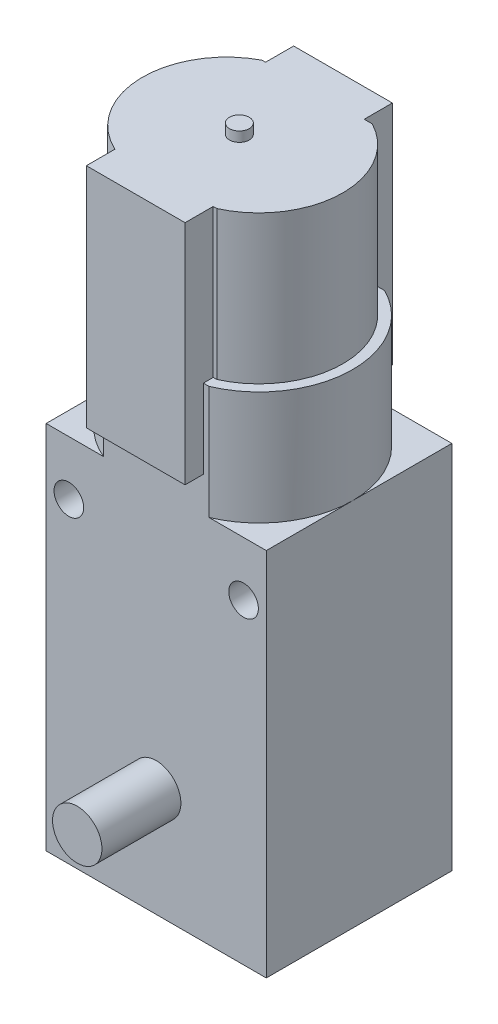
SolidWorks part; units mm, degrees
ref_plane "前视基准面" through (0, 0, 0) normal (0, 0, 1) x (1, 0, 0)
ref_plane "上视基准面" through (0, 0, 0) normal (0, 1, 0) x (1, 0, 0)
ref_plane "右视基准面" through (0, 0, 0) normal (1, 0, 0) x (0, 0, -1)
sketch "草图1" plane through (0, 0, 0) normal (0, 1, 0) x (1, 0, 0)
  line L0 (0, 0) -> (11.492, 0) construction
  line L1 (0, 0) -> (0, -13.6468) construction
  line L3 (-11.15, 9.4) -> (11.15, 9.4)
  line L4 (-11.15, 9.4) -> (-11.15, -9.4)
  line L5 (-11.15, -9.4) -> (11.15, -9.4)
  line L6 (11.15, 9.4) -> (11.15, -9.4)
  line L7 (-11.15, 9.4) -> (11.15, -9.4) construction
  line L8 (-11.15, -9.4) -> (11.15, 9.4) construction
  point P4 (0, 0)
  dimension "D1" = 22.3
  dimension "D2" = 18.8
extrude "凸台-拉伸1" add sketch "草图1" along normal blind 37.5
sketch "草图2" plane through (0, 37.5, 0) normal (0, 1, 0) x (1, 0, 0)
  line L0 (11.15, -9.4) -> (-11.15, 7.9) construction
  line L1 (11.15, -9.4) -> (-11.15, -9.4)
  line L2 (11.15, -9.4) -> (11.15, -0.6398)
  line L3 (11.15, 7.9) -> (-11.15, 7.9)
  line L4 (11.15, -9.4) -> (11.15, 9.4)
  line L5 (11.15, 9.4) -> (-11.15, 9.4)
  line L6 (-11.15, 9.4) -> (-11.15, -9.4)
  line L7 (-11.15, -9.4) -> (11.15, -9.4)
  line L8 (11.15, -9.4) -> (11.15, 9.4)
  line L9 (11.15, 9.4) -> (-11.15, 9.4)
  line L10 (-11.15, 9.4) -> (-11.15, -9.4)
  line L11 (-11.15, -9.4) -> (11.15, -9.4)
  line L12 (-11.15, -9.4) -> (-11.15, 7.9)
  line L13 (-11.15, -9.4) -> (11.15, 7.9) construction
  line L14 (-11.1286, -0.0014) -> (-11.15, 0)
  line L15 (0, -0.75) -> (0, 7.9)
  arc A1 (5.8274, 7.9) -> (5.3447, -9.4) centre (1.6378, -0.6398) cw
  arc A2 (-5.8274, 7.9) -> (-5.3447, -9.4) centre (-1.6378, -0.6398) ccw
  line M9 (11.15, -9.4) -> (11.15, 9.4)
  line M11 (-11.15, 9.4) -> (-11.15, -9.4)
  line M12 (-11.15, -9.4) -> (11.15, -9.4)
  dimension "D2" = 1.5
  dimension "D1" = 0
extrude "凸台-拉伸2" add sketch "草图2" along normal blind 11.5 contours L3 M9 M11 M12
sketch "草图3" plane through (0, 49, 0) normal (0, 1, 0) x (1, 0, 0)
  line L7 (-5.3447, -9.4) -> (5.3447, -9.4)
  line L10 (-5.1359, -8.4) -> (5.1359, -8.4)
  line L15 (5.5885, 6.9) -> (-5.5885, 6.9)
  line L17 (-5.3447, -8.4) -> (5.3447, -8.4) construction
  line L23 (-5.3447, -9.4) -> (5.3447, -9.4)
  line L28 (5.3447, -9.4) -> (-5.3447, -9.4)
  line L30 (5.3447, -9.4) -> (-5.3447, -9.4)
  line L34 (5.8274, 7.9) -> (-5.8274, 7.9)
  arc A0 (5.8274, 7.9) -> (5.3447, -9.4) centre (1.6378, -0.6398) cw
  arc A1 (-5.8274, 7.9) -> (-5.3447, -9.4) centre (-1.6378, -0.6398) ccw
  arc A2 (5.5885, 6.9) -> (5.1359, -8.4) centre (1.6378, -0.6398) cw
  arc A3 (-5.5885, 6.9) -> (-5.1359, -8.4) centre (-1.6378, -0.6398) ccw
  arc A5 (5.5885, 6.9) -> (4.955, -8.4791) centre (1.6378, -0.6398) cw construction
  arc A6 (-5.5885, 6.9) -> (-4.955, -8.4791) centre (-1.6378, -0.6398) ccw construction
  point P6 (0, -1.0733)
  dimension "D1" = 1
extrude "凸台-拉伸3" add sketch "草图3" along normal blind 15
sketch "草图6" plane through (0, 64, 0) normal (0, 1, 0) x (1, 0, 0)
  circle A1 centre (-0.2263, -0.75) radius 1
extrude "凸台-拉伸5" add sketch "草图6" along normal blind 1
sketch "草图7" plane through (0, 0, 0) normal (0, -1, 0) x (1, 0, 0)
  line L0 (-11.15, 9.4) -> (11.15, -7.9) construction
  line L1 (-11.15, 9.4) -> (11.15, 9.4)
  line L2 (-11.15, 9.4) -> (-11.15, 0.6398)
  line L3 (-11.15, -7.9) -> (11.15, -7.9)
  line L4 (-11.15, 9.4) -> (-11.15, -9.4)
  line L5 (-11.15, -9.4) -> (11.15, -9.4)
  line L6 (11.15, -9.4) -> (11.15, 9.4)
  line L7 (11.15, 9.4) -> (-11.15, 9.4)
  line L8 (11.15, 9.4) -> (11.15, -7.9)
  line L9 (11.15, 9.4) -> (-11.15, -7.9) construction
  line L10 (11.1286, 0.0014) -> (11.15, 0)
  line L11 (0, 0.75) -> (0, -7.9)
  line L13 (2.5, 2.25) -> (-2.5, 2.25)
  line L14 (2.5, 2.25) -> (2.5, -0.75)
  line L15 (2.5, -0.75) -> (-2.5, -0.75)
  line L16 (-2.5, 2.25) -> (-2.5, -0.75)
  line L17 (2.5, 2.25) -> (-2.5, -0.75) construction
  line L18 (2.5, -0.75) -> (-2.5, 2.25) construction
  arc A0 (-5.8274, -7.9) -> (-5.3447, 9.4) centre (-1.6378, 0.6398) cw
  arc A1 (5.8274, -7.9) -> (5.3447, 9.4) centre (1.6378, 0.6398) ccw
  dimension "D1" = 3
  dimension "D2" = 5
extrude "凸台-拉伸6" add sketch "草图7" along normal blind 5 contours L14 L15 L16 L13
sketch "草图8" plane through (0, 0, 2.25) normal (0, 0, 1) x (1, 0, 0)
  line L0 (-2.5, 0) -> (2.5, -5)
  circle A0 centre (0, -2.5) radius 1.5
  dimension "D1" = 3
extrude "切除-拉伸1" cut sketch "草图8" against normal through all contours L0 A0 | L0 A0
sketch "草图9" plane through (0, 0, -9.4) normal (0, 0, -1) x (-1, 0, 0)
  line L0 (-11.15, 0) -> (11.15, 0) construction
  line L1 (-2.6, 11) -> (0, 13.6)
  line L3 (2.6, 11) -> (0, 8.4)
  line L4 (-11.15, 37.5) -> (11.15, 37.5)
  line L5 (-11.15, 37.5) -> (-11.15, 0)
  line L6 (-11.15, 0) -> (11.15, 0)
  line L7 (11.15, 37.5) -> (11.15, 0)
  arc A0 (-2.6, 11) -> (0, 8.4) centre (0, 11) ccw
  circle A1 centre (0, 11) radius 1
  arc A2 (2.6, 11) -> (0, 13.6) centre (0, 11) ccw
  dimension "D1" = 11
extrude "凸台-拉伸7" add sketch "草图9" along normal blind 8 contours L3 A2 L1 A0 A1
sketch "草图10" plane through (0, 0, 9.4) normal (0, 0, 1) x (1, 0, 0)
  line L2 (-11.15, 37.5) -> (11.15, 37.5)
  line L3 (-11.15, 37.5) -> (-11.15, 0)
  line L4 (-11.15, 0) -> (11.15, 0)
  line L5 (11.15, 37.5) -> (11.15, 0)
  circle A1 centre (0, 11) radius 2.5
  dimension "D1" = 5
extrude "凸台-拉伸8" add sketch "草图10" along normal blind 8 contours A1
sketch "草图11" plane through (0, 64, 0) normal (0, 1, 0) x (1, 0, 0)
  line L0 (-5.2263, -6.7052) -> (-5.2263, -11.25)
  line L2 (-0.2263, 9.75) -> (-5.2263, 9.75)
  line L3 (-0.2263, 9.75) -> (4.7737, 9.75)
  line L4 (-5.2263, 9.75) -> (-5.2263, 5.2052)
  line L5 (4.7737, 9.75) -> (4.7737, 5.2052)
  line L6 (-5.2263, -11.25) -> (4.7737, -11.25)
  line L8 (4.7737, -6.7052) -> (4.7737, -11.25)
  arc A0 (-5.2263, 5.2052) -> (-5.2263, -6.7052) centre (-0.2263, -0.75) ccw
  arc A1 (4.7737, -6.7052) -> (4.7737, 5.2052) centre (-0.2263, -0.75) ccw
  dimension "D1" = 10.5
  dimension "D3" = 5
  dimension "D4" = 5
extrude "凸台-拉伸9" add sketch "草图11" against normal blind 23
sketch "草图12" plane through (0, 0, -9.4) normal (0, 0, -1) x (-1, 0, 0)
  line L0 (-11.15, 37.5) -> (-11.15, 0) construction
  line L1 (-11.15, 37.5) -> (11.15, 37.5) construction
  line L2 (11.15, 37.5) -> (11.15, 0) construction
  circle A0 centre (-8.85, 32) radius 1.5
  circle A1 centre (8.85, 32) radius 1.5
  dimension "D1" = 3
  dimension "D4" = 3
  dimension "D2" = 2.3
  dimension "D3" = 5.5
  dimension "D5" = 2.3
  dimension "D6" = 5.5
extrude "切除-拉伸2" cut sketch "草图12" against normal through all
sketch "草图13" plane through (0, 0, -9.4) normal (0, 0, -1) x (-1, 0, 0)
  line L1 (-11.15, 37.5) -> (11.15, 37.5)
  line L2 (-11.15, 37.5) -> (-11.15, 0)
  line L3 (-11.15, 0) -> (11.15, 0)
  line L4 (11.15, 37.5) -> (11.15, 0)
  circle A0 centre (-8.85, 32) radius 1.5
  circle A1 centre (8.85, 32) radius 1.5
  circle A2 centre (0, 11) radius 2.6
  circle A3 centre (0, -2.5) radius 1.5
